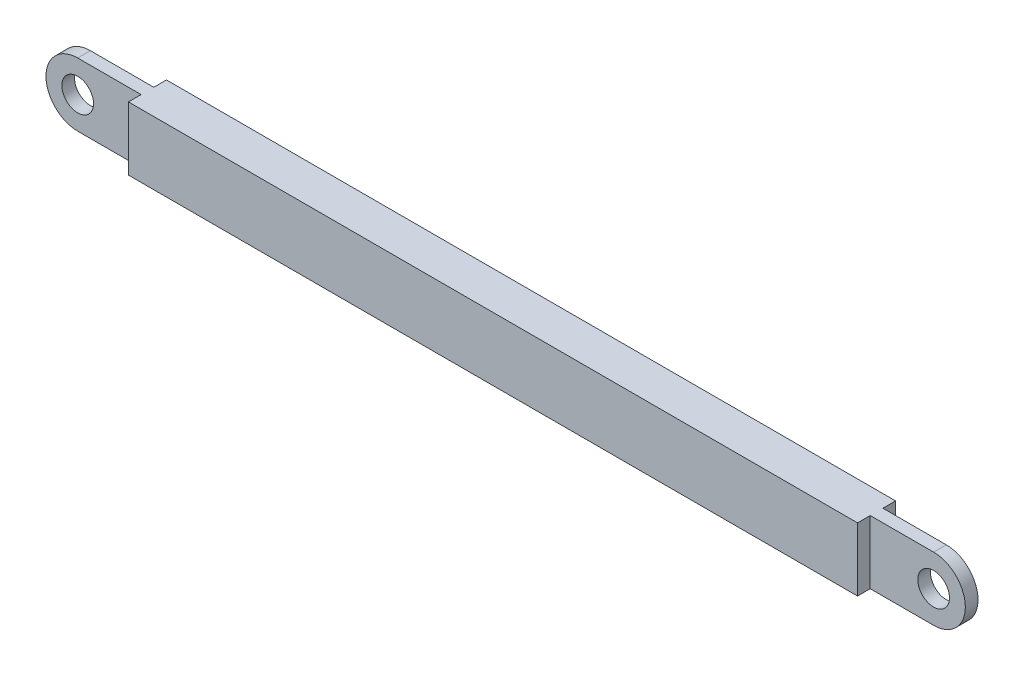
SolidWorks part; units mm, degrees
ref_plane "Спереди" through (0, 0, 0) normal (0, 0, 1) x (1, 0, 0)
ref_plane "Сверху" through (0, 0, 0) normal (0, 1, 0) x (1, 0, 0)
ref_plane "Справа" through (0, 0, 0) normal (1, 0, 0) x (0, 0, -1)
other "Configuration Table"
sketch "Sketch19" plane through (0, 0, 0) normal (0, 0, 1) x (1, 0, 0)
  line L0 (0, -5) -> (0, 5) construction
  line L1 (57.5, -5) -> (-57.5, -5)
  line L2 (57.5, -5) -> (57.5, 5)
  line L3 (57.5, 5) -> (-57.5, 5)
  line L4 (-57.5, -5) -> (-57.5, 5)
  line L5 (57.5, -5) -> (-57.5, 5) construction
  line L6 (57.5, 5) -> (-57.5, -5) construction
  point P0 (0, 0)
  point P6 (0, -5)
  point P8 (0, 5)
  dimension "D1" = 115
  dimension "D2" = 10
extrude "Boss-Extrude4" add sketch "Sketch19" along normal mid plane 6 contours L3 L4 L1 L2
sketch3d "3DSketch5" plane through (0, 0, 0) normal (0, 0, 1) x (1, 0, 0)
sketch3d "3DSketch8"
  line L0 (0, -5, 0) -> (0, 5, 0) construction
ref_plane "Plane12" through (0, 0, 0) normal (1, 0, 0) x (0, 0, -1)
sketch "Sketch22" plane through (0, 0, 0) normal (0, 0, 1) x (1, 0, 0)
  line L0 (57.5, 5) -> (67.5, 5)
  line L2 (57.5, -5) -> (67.5, -5)
  line L3 (57.5, 5) -> (57.5, -5)
  arc A0 (67.5, 5) -> (67.5, -5) centre (67.5, 0) cw
  circle A1 centre (67.5, 0) radius 2.5
  dimension "D1" = 10
  dimension "D2" = 5
extrude "Boss-Extrude5" add sketch "Sketch22" along normal mid plane 2 contours L0 A0 L2 L3
mirror "Mirror1" about plane through (0, 0, 0) normal (1, 0, 0) of "Boss-Extrude4", "Boss-Extrude5"
